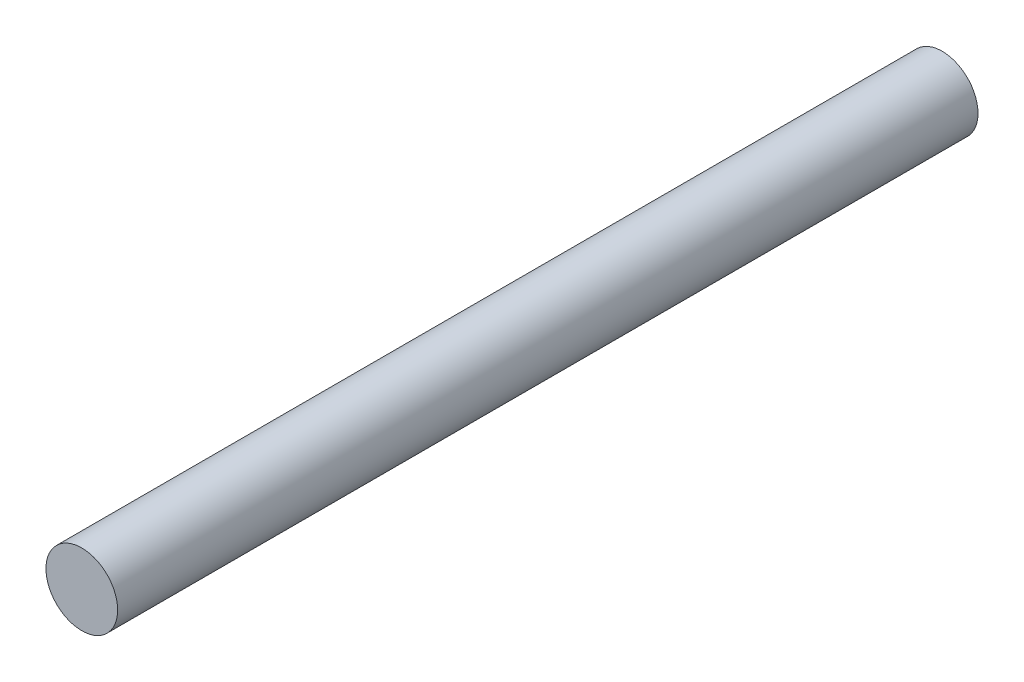
SolidWorks part; units mm, degrees
ref_plane "Front Plane" through (0, 0, 0) normal (0, 0, 1) x (1, 0, 0)
ref_plane "Top Plane" through (0, 0, 0) normal (0, 1, 0) x (1, 0, 0)
ref_plane "Right Plane" through (0, 0, 0) normal (1, 0, 0) x (0, 0, -1)
sketch "Sketch1" plane through (0, 0, 0) normal (0, 0, 1) x (1, 0, 0)
  circle A0 centre (0, 0) radius 6.25
  dimension "D1" = 12.5
extrude "Boss-Extrude2" add sketch "Sketch1" along normal blind 150
